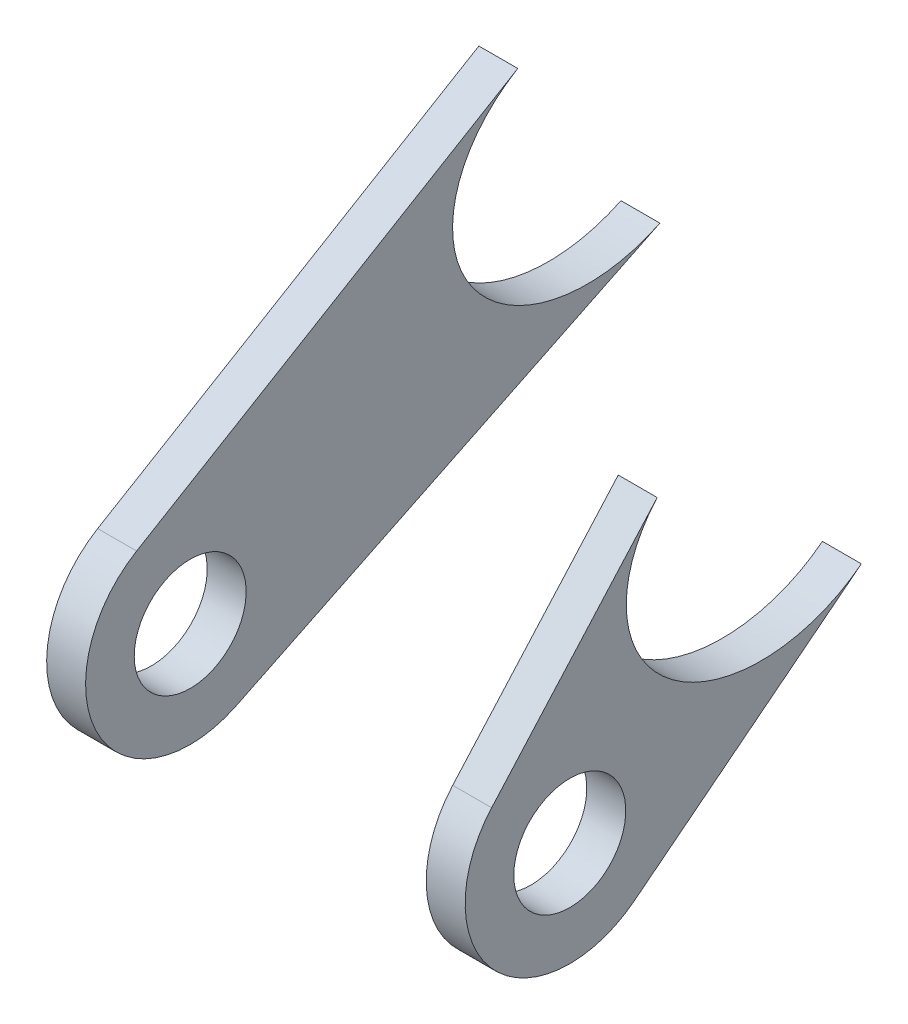
SolidWorks part; units mm, degrees
material "1.0545 (S355N)"
ref_plane "Płaszczyzna XY" through (0, 0, 0) normal (0, 0, 1) x (1, 0, 0)
ref_plane "Płaszczyzna XZ" through (0, 0, 0) normal (0, 1, 0) x (1, 0, 0)
ref_plane "Płaszczyzna YZ" through (0, 0, 0) normal (1, 0, 0) x (0, 0, -1)
ref_plane "Płaszczyzna1" through (-28.6854, 0, 0) normal (-1, 0, 0) x (0, 0, 1)
sketch "Szkic1" plane through (-28.6854, 0, 0) normal (-1, 0, 0) x (0, 0, 1)
  line L0 (508.7365, -278.2324) -> (465.183, -257.0383)
  line L1 (518.9464, -259.3332) -> (479.7828, -235.9777)
  circle A0 centre (513.4403, -268.5661) radius 5.75
  arc A1 (508.7365, -278.2324) -> (518.9464, -259.3332) centre (513.4403, -268.5661) ccw
  circle A2 centre (513.4403, -268.5661) radius 10.75 construction
  spline S1 degree 3 poles (457.4122, -243.8245) (461.4326, -219.1499) (490.3653, -223.8642) (486.3449, -248.5388) (482.3244, -273.2134) (453.3917, -268.4991) (457.4122, -243.8245) (461.4326, -219.1499) (490.3653, -223.8642) knots -0.5 0 0 0 0.5 0.5 0.5 1 1 1 1.5 1.5 1.5 weights 1 0.333333 0.333333 1 0.333333 0.333333 1 0.333333 0.333333 only from (457.4122, -243.8245) to (457.4122, -243.8245)
  dimension "D1" = 11.5
  dimension "D2" = 5
extrude "Dodanie-wyciągnięcie1" add sketch "Szkic1" along normal blind 4 contours L1 S1 L0 A1 A0
ref_plane "Płaszczyzna2" through (6.3146, 0, 0) normal (-1, 0, 0) x (0, 0, 1)
sketch "Szkic2" plane through (6.3146, 0, 0) normal (-1, 0, 0) x (0, 0, 1)
  line L0 (506.8, -277.02) -> (483.483, -258.7051)
  line L1 (521.4686, -261.417) -> (504.459, -242.3156)
  circle A0 centre (513.4403, -268.5661) radius 5.75
  arc A1 (506.8, -277.02) -> (521.4686, -261.417) centre (513.4403, -268.5661) ccw
  circle A2 centre (513.4403, -268.5661) radius 10.75 construction
  spline S1 degree 3 poles (478.5639, -247.271) (482.5844, -222.5964) (511.5171, -227.3106) (507.4966, -251.9852) (503.4762, -276.6598) (474.5435, -271.9456) (478.5639, -247.271) (482.5844, -222.5964) (511.5171, -227.3106) knots -0.5 0 0 0 0.5 0.5 0.5 1 1 1 1.5 1.5 1.5 weights 1 0.333333 0.333333 1 0.333333 0.333333 1 0.333333 0.333333 only from (478.5639, -247.271) to (478.5639, -247.271)
  dimension "D1" = 11.5
  dimension "D2" = 5
extrude "Dodanie-wyciągnięcie2" add sketch "Szkic2" against normal blind 4 separate body contours L1 S1 L0 A1 A0
